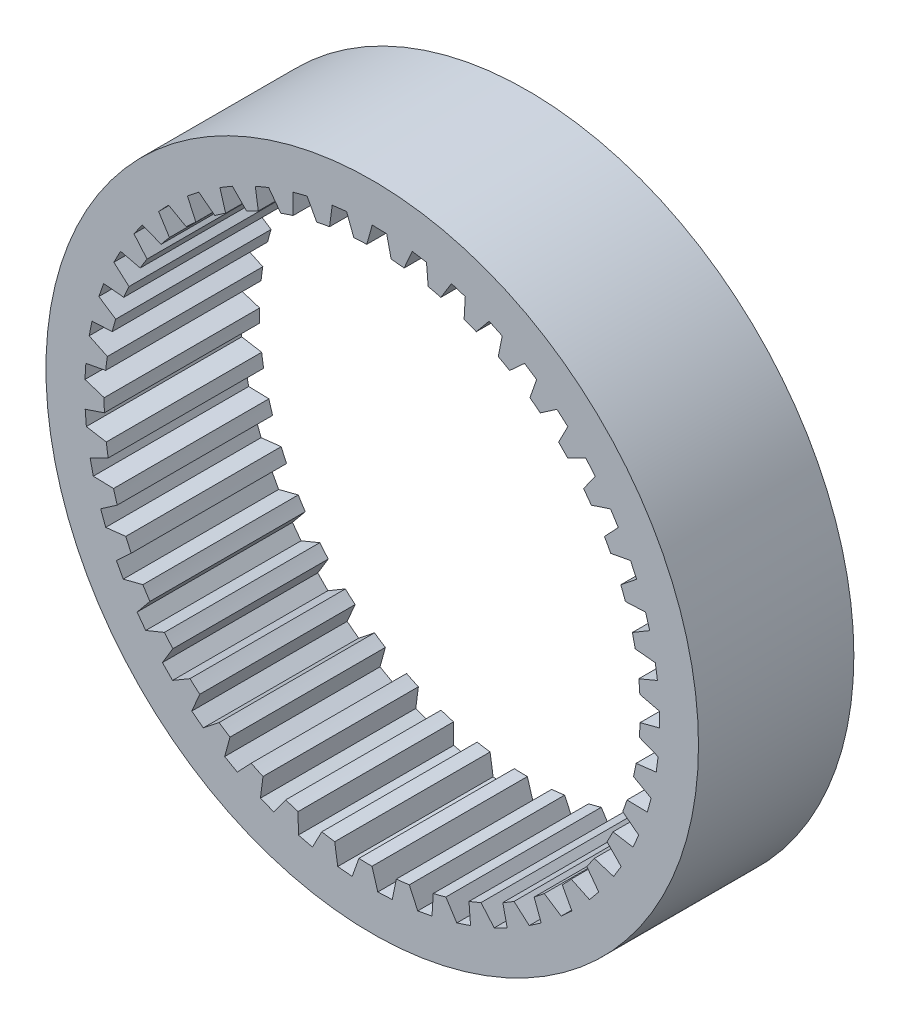
SolidWorks part; units mm, degrees
ref_plane "Front Plane" through (0, 0, 0) normal (0, 0, 1) x (1, 0, 0)
ref_plane "Top Plane" through (0, 0, 0) normal (0, 1, 0) x (1, 0, 0)
ref_plane "Right Plane" through (0, 0, 0) normal (1, 0, 0) x (0, 0, -1)
sketch "Sketch1" plane through (0, 0, 0) normal (0, 0, 1) x (1, 0, 0)
  line L0 (-0.825, 18.4816) -> (-0.7693, 17.2328) construction
  line L130 (-1.1886, 17.209) -> (-1.6484, 18.4264)
  line L131 (-0.3495, 17.2465) -> (0, 18.5)
  line L132 (1.218, 17.2069) -> (0.9321, 18.4765)
  line L133 (2.0542, 17.1273) -> (2.5747, 18.32)
  line L134 (3.6009, 16.87) -> (3.4945, 18.167)
  line L135 (4.4178, 16.6747) -> (5.0993, 17.7833)
  line L136 (5.9137, 16.2046) -> (5.9888, 17.5038)
  line L137 (6.6955, 15.8976) -> (7.5246, 16.9006)
  line L138 (8.1114, 15.2239) -> (8.3666, 16.5)
  line L139 (8.8429, 14.811) -> (9.8035, 15.6889)
  line L140 (10.1512, 13.9469) -> (10.5816, 15.175)
  line L141 (10.8181, 13.4362) -> (11.8916, 14.1718)
  line L142 (11.9935, 12.3984) -> (12.5905, 13.5546)
  line L143 (12.5828, 11.7998) -> (13.7482, 12.3789)
  line L144 (13.6023, 10.6085) -> (14.3544, 11.6705)
  line L145 (14.1025, 9.9338) -> (15.3372, 10.3451)
  line L146 (14.9463, 8.6122) -> (15.839, 9.5591)
  line L147 (15.3478, 7.8745) -> (16.6277, 8.1099)
  line L148 (15.9994, 6.4483) -> (17.0152, 7.2618)
  line L149 (16.2944, 5.6618) -> (17.5945, 5.7168)
  line L150 (16.7412, 4.1588) -> (17.8602, 4.823)
  line L151 (16.9238, 3.339) -> (18.2189, 3.2125)
  line L152 (17.157, 1.7884) -> (18.3577, 2.2904)
  line L153 (17.2238, 0.9512) -> (18.4887, 0.6456)
  line L154 (17.239, -0.6168) -> (18.4978, -0.2868)
  line L155 (17.1885, -1.4552) -> (18.3987, -1.9338)
  line L156 (16.9854, -3.01) -> (18.2778, -2.8584)
  line L157 (16.8187, -3.8332) -> (17.9505, -4.4756)
  line L158 (16.4012, -5.3446) -> (17.7022, -5.3743)
  line L159 (16.1216, -6.1366) -> (17.1529, -6.9302)
  line L160 (15.4977, -7.5752) -> (16.7819, -7.7857)
  line L161 (15.1106, -8.3206) -> (16.0215, -9.25)
  line L162 (14.2926, -9.6583) -> (15.535, -10.0455)
  line L163 (13.8056, -10.3426) -> (14.5782, -11.3897)
  line L164 (12.8094, -11.5535) -> (13.9858, -12.1098)
  line L165 (12.2318, -12.1633) -> (12.8512, -13.3078)
  line L166 (11.0768, -13.2237) -> (12.1643, -13.9384)
  line L167 (10.4199, -13.7473) -> (10.874, -14.9668)
  line L168 (9.1286, -14.6366) -> (10.1061, -15.4957)
  line L169 (8.4053, -15.0637) -> (8.6852, -16.3345)
  line L170 (7.0027, -15.7647) -> (7.8512, -16.7514)
  line L171 (6.227, -16.0868) -> (6.3274, -17.3843)
  line L172 (4.7406, -16.5858) -> (5.4434, -17.681)
  line L173 (3.9276, -16.7969) -> (3.8464, -18.0957)
  line L174 (2.3861, -17.0842) -> (2.9297, -18.2665)
  line L175 (1.5517, -17.1801) -> (1.2905, -18.4549)
  line L176 (-0.0148, -17.25) -> (0.359, -18.4965)
  line L177 (-0.8544, -17.2288) -> (-1.2905, -18.4549)
  line L178 (-2.4153, -17.0801) -> (-2.2187, -18.3665)
  line L179 (-3.2439, -16.9422) -> (-3.8464, -18.0957)
  line L180 (-4.7689, -16.5777) -> (-4.7533, -17.8789)
  line L181 (-5.5702, -16.3259) -> (-6.3274, -17.3843)
  line L182 (-7.0297, -15.7527) -> (-7.1953, -17.0434)
  line L183 (-7.7882, -15.3918) -> (-8.6852, -16.3345)
  line L184 (-9.1536, -14.621) -> (-9.4972, -15.8762)
  line L185 (-9.8545, -14.1581) -> (-10.874, -14.9668)
  line L186 (-11.0994, -13.2048) -> (-11.6143, -14.3999)
  line L187 (-11.729, -12.6488) -> (-12.8512, -13.3078)
  line L188 (-12.8291, -11.5315) -> (-13.5054, -12.6434)
  line L189 (-13.3752, -10.8934) -> (-14.5782, -11.3897)
  line L190 (-14.3091, -9.6338) -> (-15.1336, -10.6407)
  line L191 (-14.7611, -8.9259) -> (-16.0215, -9.25)
  line L192 (-15.5107, -7.5486) -> (-16.4672, -8.431)
  line L193 (-15.8597, -6.7847) -> (-17.1529, -6.9302)
  line L194 (-16.4103, -5.3165) -> (-17.4803, -6.0571)
  line L195 (-16.6496, -4.5114) -> (-17.9505, -4.4756)
  line L196 (-16.9905, -2.9809) -> (-18.1532, -3.5654)
  line L197 (-17.1155, -2.1503) -> (-18.3987, -1.9338)
  line L198 (-17.24, -0.5873) -> (-18.4727, -1.0043)
  line L199 (-17.2482, 0.2526) -> (-18.4887, 0.6456)
  line L200 (-17.154, 1.8178) -> (-18.4327, 1.5764)
  line L201 (-17.0451, 2.6506) -> (-18.2189, 3.2125)
  line L202 (-16.734, 4.1875) -> (-18.0339, 4.1264)
  line L203 (-16.5104, 4.9971) -> (-17.5945, 5.7168)
  line L204 (-15.9884, 6.4756) -> (-17.2841, 6.5961)
  line L205 (-15.6542, 7.2462) -> (-16.6277, 8.1099)
  line L206 (-14.9316, 8.6378) -> (-16.1979, 8.9374)
  line L207 (-14.4934, 9.3544) -> (-15.3372, 10.3451)
  line L208 (-13.5841, 10.6318) -> (-14.7965, 11.1047)
  line L209 (-13.0505, 11.2804) -> (-13.7482, 12.3789)
  line L210 (-11.9722, 12.4189) -> (-13.107, 13.0559)
  line L211 (-11.3535, 12.9869) -> (-11.8916, 14.1718)
  line L212 (-10.1274, 13.9642) -> (-11.1624, 14.753)
  line L213 (-9.4356, 14.4406) -> (-9.8035, 15.6889)
  line L214 (-8.0854, 15.2378) -> (-9.0006, 16.1629)
  line L215 (-7.334, 15.6133) -> (-7.5246, 16.9006)
  line L216 (-5.886, 16.2147) -> (-6.6635, 17.2583)
  line L217 (-5.0897, 16.482) -> (-5.0993, 17.7833)
  line L218 (-3.572, 16.8761) -> (-4.1968, 18.0177)
  line L219 (-2.7463, 17.03) -> (-2.5747, 18.32)
  line L220 (-2.5747, 18.32) -> (-1.6484, 18.4264)
  line L221 (0, 18.5) -> (0.9321, 18.4765)
  line L222 (2.5747, 18.32) -> (3.4945, 18.167)
  line L223 (5.0993, 17.7833) -> (5.9888, 17.5038)
  line L224 (7.5246, 16.9006) -> (8.3666, 16.5)
  line L225 (9.8035, 15.6889) -> (10.5816, 15.175)
  line L226 (11.8916, 14.1718) -> (12.5905, 13.5546)
  line L227 (13.7482, 12.3789) -> (14.3544, 11.6705)
  line L228 (15.3372, 10.3451) -> (15.839, 9.5591)
  line L229 (16.6277, 8.1099) -> (17.0152, 7.2618)
  line L230 (17.5945, 5.7168) -> (17.8602, 4.823)
  line L231 (18.2189, 3.2125) -> (18.3577, 2.2904)
  line L232 (18.4887, 0.6456) -> (18.4978, -0.2868)
  line L233 (18.3987, -1.9338) -> (18.2778, -2.8584)
  line L234 (17.9505, -4.4756) -> (17.7022, -5.3743)
  line L235 (17.1529, -6.9302) -> (16.7819, -7.7857)
  line L236 (16.0215, -9.25) -> (15.535, -10.0455)
  line L237 (14.5782, -11.3897) -> (13.9858, -12.1098)
  line L238 (12.8512, -13.3078) -> (12.1643, -13.9384)
  line L239 (10.874, -14.9668) -> (10.1061, -15.4957)
  line L240 (8.6852, -16.3345) -> (7.8512, -16.7514)
  line L241 (6.3274, -17.3843) -> (5.4434, -17.681)
  line L242 (3.8464, -18.0957) -> (2.9297, -18.2665)
  line L243 (1.2905, -18.4549) -> (0.359, -18.4965)
  line L244 (-1.2905, -18.4549) -> (-2.2187, -18.3665)
  line L245 (-3.8464, -18.0957) -> (-4.7533, -17.8789)
  line L246 (-6.3274, -17.3843) -> (-7.1953, -17.0434)
  line L247 (-8.6852, -16.3345) -> (-9.4972, -15.8762)
  line L248 (-10.874, -14.9668) -> (-11.6143, -14.3999)
  line L249 (-12.8512, -13.3078) -> (-13.5054, -12.6434)
  line L250 (-14.5782, -11.3897) -> (-15.1336, -10.6407)
  line L251 (-16.0215, -9.25) -> (-16.4672, -8.431)
  line L252 (-17.1529, -6.9302) -> (-17.4803, -6.0571)
  line L253 (-17.9505, -4.4756) -> (-18.1532, -3.5654)
  line L254 (-18.3987, -1.9338) -> (-18.4727, -1.0043)
  line L255 (-18.4887, 0.6456) -> (-18.4327, 1.5764)
  line L256 (-18.2189, 3.2125) -> (-18.0339, 4.1264)
  line L257 (-17.5945, 5.7168) -> (-17.2841, 6.5961)
  line L258 (-16.6277, 8.1099) -> (-16.1979, 8.9374)
  line L259 (-15.3372, 10.3451) -> (-14.7965, 11.1047)
  line L260 (-13.7482, 12.3789) -> (-13.107, 13.0559)
  line L261 (-11.8916, 14.1718) -> (-11.1624, 14.753)
  line L262 (-9.8035, 15.6889) -> (-9.0006, 16.1629)
  line L263 (-7.5246, 16.9006) -> (-6.6635, 17.2583)
  line L264 (-5.0993, 17.7833) -> (-4.1968, 18.0177)
  circle A46 centre (0, 0) radius 21
  circle A47 centre (0, 0) radius 18.5 construction
  circle A48 centre (0, 0) radius 17.25 construction
  arc A49 (0, 18.5) -> (-1.6484, 18.4264) centre (0, 0) ccw construction
  arc A50 (-0.3495, 17.2465) -> (-1.1886, 17.209) centre (0, 0) ccw
  arc A51 (2.0542, 17.1273) -> (1.218, 17.2069) centre (0, 0) ccw
  arc A52 (4.4178, 16.6747) -> (3.6009, 16.87) centre (0, 0) ccw
  arc A53 (6.6955, 15.8976) -> (5.9137, 16.2046) centre (0, 0) ccw
  arc A54 (8.8429, 14.811) -> (8.1114, 15.2239) centre (0, 0) ccw
  arc A55 (10.8181, 13.4362) -> (10.1512, 13.9469) centre (0, 0) ccw
  arc A56 (12.5828, 11.7998) -> (11.9935, 12.3984) centre (0, 0) ccw
  arc A57 (14.1025, 9.9338) -> (13.6023, 10.6085) centre (0, 0) ccw
  arc A58 (15.3478, 7.8745) -> (14.9463, 8.6122) centre (0, 0) ccw
  arc A59 (16.2944, 5.6618) -> (15.9994, 6.4483) centre (0, 0) ccw
  arc A60 (16.9238, 3.339) -> (16.7412, 4.1588) centre (0, 0) ccw
  arc A61 (17.2238, 0.9512) -> (17.157, 1.7884) centre (0, 0) ccw
  arc A62 (17.1885, -1.4552) -> (17.239, -0.6168) centre (0, 0) ccw
  arc A63 (16.8187, -3.8332) -> (16.9854, -3.01) centre (0, 0) ccw
  arc A64 (16.1216, -6.1366) -> (16.4012, -5.3446) centre (0, 0) ccw
  arc A65 (15.1106, -8.3206) -> (15.4977, -7.5752) centre (0, 0) ccw
  arc A66 (13.8056, -10.3426) -> (14.2926, -9.6583) centre (0, 0) ccw
  arc A67 (12.2318, -12.1633) -> (12.8094, -11.5535) centre (0, 0) ccw
  arc A68 (10.4199, -13.7473) -> (11.0768, -13.2237) centre (0, 0) ccw
  arc A69 (8.4053, -15.0637) -> (9.1286, -14.6366) centre (0, 0) ccw
  arc A70 (6.227, -16.0868) -> (7.0027, -15.7647) centre (0, 0) ccw
  arc A71 (3.9276, -16.7969) -> (4.7406, -16.5858) centre (0, 0) ccw
  arc A72 (1.5517, -17.1801) -> (2.3861, -17.0842) centre (0, 0) ccw
  arc A73 (-0.8544, -17.2288) -> (-0.0148, -17.25) centre (0, 0) ccw
  arc A74 (-3.2439, -16.9422) -> (-2.4153, -17.0801) centre (0, 0) ccw
  arc A75 (-5.5702, -16.3259) -> (-4.7689, -16.5777) centre (0, 0) ccw
  arc A76 (-7.7882, -15.3918) -> (-7.0297, -15.7527) centre (0, 0) ccw
  arc A77 (-9.8545, -14.1581) -> (-9.1536, -14.621) centre (0, 0) ccw
  arc A78 (-11.729, -12.6488) -> (-11.0994, -13.2048) centre (0, 0) ccw
  arc A79 (-13.3752, -10.8934) -> (-12.8291, -11.5315) centre (0, 0) ccw
  arc A80 (-14.7611, -8.9259) -> (-14.3091, -9.6338) centre (0, 0) ccw
  arc A81 (-15.8597, -6.7847) -> (-15.5107, -7.5486) centre (0, 0) ccw
  arc A82 (-16.6496, -4.5114) -> (-16.4103, -5.3165) centre (0, 0) ccw
  arc A83 (-17.1155, -2.1503) -> (-16.9905, -2.9809) centre (0, 0) ccw
  arc A84 (-17.2482, 0.2526) -> (-17.24, -0.5873) centre (0, 0) ccw
  arc A85 (-17.0451, 2.6506) -> (-17.154, 1.8178) centre (0, 0) ccw
  arc A86 (-16.5104, 4.9971) -> (-16.734, 4.1875) centre (0, 0) ccw
  arc A87 (-15.6542, 7.2462) -> (-15.9884, 6.4756) centre (0, 0) ccw
  arc A88 (-14.4934, 9.3544) -> (-14.9316, 8.6378) centre (0, 0) ccw
  arc A89 (-13.0505, 11.2804) -> (-13.5841, 10.6318) centre (0, 0) ccw
  arc A90 (-11.3535, 12.9869) -> (-11.9722, 12.4189) centre (0, 0) ccw
  arc A91 (-9.4356, 14.4406) -> (-10.1274, 13.9642) centre (0, 0) ccw
  arc A92 (-7.334, 15.6133) -> (-8.0854, 15.2378) centre (0, 0) ccw
  arc A93 (-5.0897, 16.482) -> (-5.886, 16.2147) centre (0, 0) ccw
  arc A94 (-2.7463, 17.03) -> (-3.572, 16.8761) centre (0, 0) ccw
  point P189 (0, 0)
  point P278 (0, 0)
  dimension "D1" = 37
  dimension "D2" = 34.5
  dimension "D3" = 1.65
  dimension "D4" = 0.42
  dimension "D6" = 42
  dimension "D5" = 0.42
extrude "Boss-Extrude2" add sketch "Sketch1" along normal blind 10
